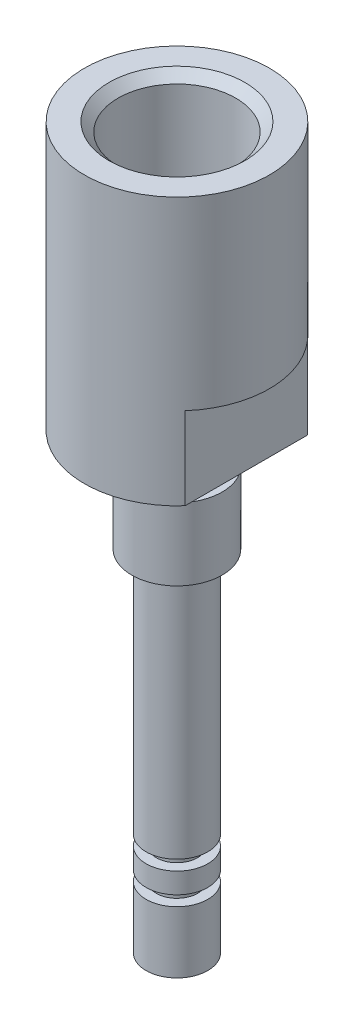
SolidWorks part; units mm, degrees
material "1.4401 (X5CrNiMo17-12-2)"
ref_plane "Ebene vorne" through (0, 0, 0) normal (0, 0, 1) x (1, 0, 0)
ref_plane "Ebene oben" through (0, 0, 0) normal (0, 1, 0) x (1, 0, 0)
ref_plane "Ebene rechts" through (0, 0, 0) normal (1, 0, 0) x (0, 0, -1)
sketch "Sketch1" plane through (0, 0, 0) normal (0, 0, 1) x (1, 0, 0)
  line L0 (0, 0) -> (0, 60.3877) construction
  line L1 (-0.75, 0) -> (-0.75, 70)
  line L2 (-0.75, 70) -> (-9, 70)
  line L3 (-9, 70) -> (-9, 44)
  line L6 (-4.396, 34) -> (-3, 34)
  line L7 (-3, 34) -> (-3, 10)
  line L8 (-3, 10) -> (-2, 10)
  line L9 (-2, 10) -> (-2, 9)
  line L10 (-2, 9) -> (-3, 9)
  line L11 (-3, 9) -> (-3, 7)
  line L12 (-3, 7) -> (-2, 7)
  line L13 (-2, 7) -> (-2, 6)
  line L14 (-2, 6) -> (-3, 6)
  line L15 (-3, 6) -> (-3, 0)
  line L16 (-3, 0) -> (-0.75, 0)
  line L17 (-4.396, 34) -> (-4.396, 41)
  line L18 (-4.396, 41) -> (-3, 41)
  line L19 (-3, 41) -> (-3, 44)
  line L20 (-9, 44) -> (-3, 44)
  dimension "D2" = 3
  dimension "D1" = 10
  dimension "D3" = 3
  dimension "D4" = 26
  dimension "D5" = 44
  dimension "D6" = 6
  dimension "D7" = 1
  dimension "D8" = 1
  dimension "D9" = 1
  dimension "D10" = 0.75
  dimension "D11" = 2
  dimension "D12" = 4.396
  dimension "D13" = 9
revolve "Revolve1" add sketch "Sketch1" angle 360 about L0
sketch "Sketch17" plane through (0, 70, 0) normal (0, 1, 0) x (1, 0, 0)
  circle A0 centre (0, 0) radius 1.5
  dimension "D1" = 3
extrude "Cut-Extrude1" cut sketch "Sketch17" against normal offset from surface (65 mm away) 5 up to face at (0, 0, -0.75)
hole_wizard "G1/4 Tapped Hole1" positions "Sketch2" profile "Sketch3" tap size "G1/4" standard "DIN"
sketch "Sketch2" plane through (0, 70, 0) normal (0, 1, 0) x (1, 0, 0)
  point P0 (0, 0)
sketch "Sketch3" plane through (0, 70, 0) normal (1, 0, 0) x (0, 0, 1)
  line L0 (0, 0) -> (0, 25.4384)
  line L1 (0, 25.4384) -> (5.7225, 22)
  line L2 (5.7225, 22) -> (5.7225, 0.881)
  line L3 (5.7225, 0.881) -> (6.6035, 0)
  line L5 (6.6035, 0) -> (0, 0)
  line L6 (-5.7225, 0.881) -> (-6.6035, 0) construction
  line L10 (0, 25.4384) -> (-5.7225, 22) construction
  line L11 (0, -6.35) -> (0, 107.95) construction
  dimension "Tap Drill Dia." = 11.445
  dimension "Tap Drill Depth" = 22
  dimension "Near C'Sink Dia." = 13.207
  dimension "Near C'Sink Angle" = 90
  dimension "Drill Angle" = 118
cosmetic thread "Hole Thread1" parameters "D1"=15, "D2"=13.157
sketch "Sketch18" plane through (0, 44, 0) normal (0, -1, 0) x (1, 0, 0)
  line L0 (0, 0) -> (0, 10.0946) construction
  line L1 (-20.3456, -8.0357) -> (-6.75, -8.0357)
  line L2 (-20.3456, -8.0357) -> (-20.3456, 8.0357)
  line L3 (-20.3456, 8.0357) -> (-6.75, 8.0357)
  line L4 (-6.75, -8.0357) -> (-6.75, 8.0357)
  line L5 (-20.3456, -8.0357) -> (-6.75, 8.0357) construction
  line L6 (-20.3456, 8.0357) -> (-6.75, -8.0357) construction
  line L7 (20.3456, 8.0357) -> (6.75, -8.0357) construction
  line L8 (20.3456, -8.0357) -> (6.75, 8.0357) construction
  line L9 (6.75, -8.0357) -> (6.75, 8.0357)
  line L10 (20.3456, 8.0357) -> (6.75, 8.0357)
  line L11 (20.3456, -8.0357) -> (20.3456, 8.0357)
  line L12 (20.3456, -8.0357) -> (6.75, -8.0357)
  point P0 (-13.5478, 0)
  point P12 (13.5478, 0)
  dimension "D1" = 6.75
extrude "Cut-Extrude2" cut sketch "Sketch18" against normal blind 8
equation "\"D8@Sketch1\"=\"D7@Sketch1\""
